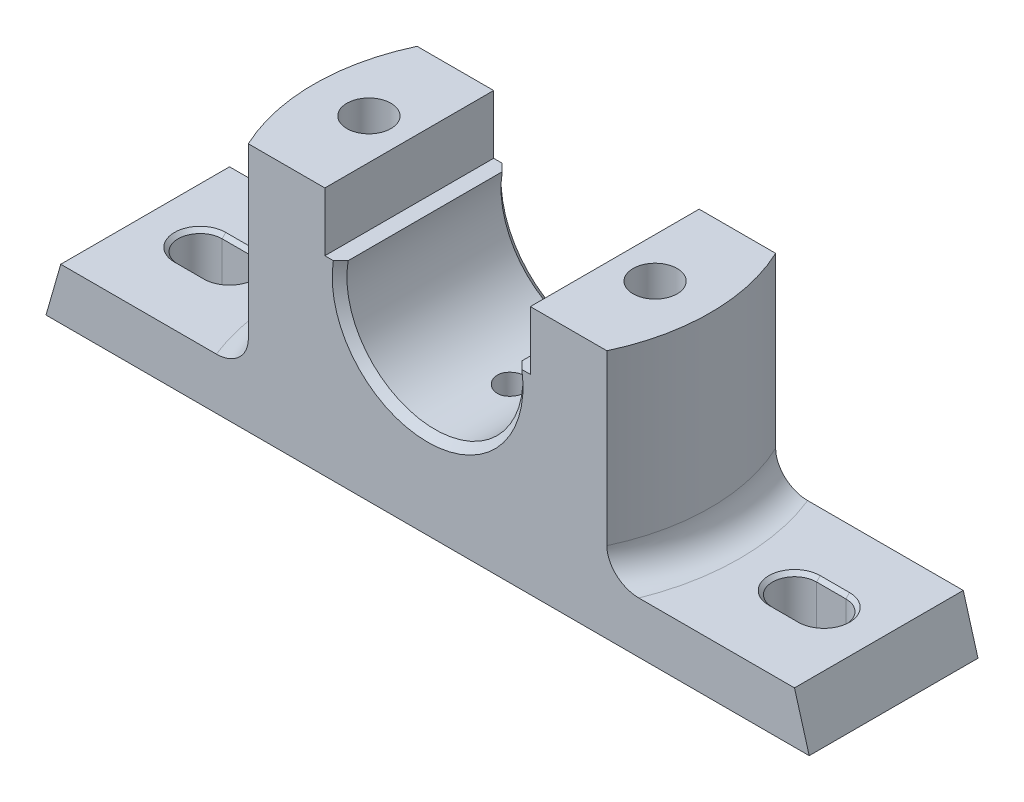
SolidWorks part; units mm, degrees
material "Plain Carbon Steel"
ref_plane "Front Plane" through (0, 0, 0) normal (0, 0, 1) x (1, 0, 0)
ref_plane "Top Plane" through (0, 0, 0) normal (0, 1, 0) x (1, 0, 0)
ref_plane "Right Plane" through (0, 0, 0) normal (1, 0, 0) x (0, 0, -1)
sketch "Sketch1" plane through (0, 0, 0) normal (0, 0, 1) x (1, 0, 0)
  line L0 (-104, 0) -> (104, 0)
  line L1 (-104, 0) -> (-99.9856, 14)
  line L2 (-99.9856, 14) -> (99.9856, 14)
  line L3 (99.9856, 14) -> (104, 0)
  line L4 (0, 0) -> (0, 50.2731) construction
  point P4 (0, 0)
  dimension "D1" = 208
  dimension "D2" = 74
  dimension "D3" = 14
extrude "Boss-Extrude1" add sketch "Sketch1" along normal mid plane 46
sketch "Sketch2" plane through (0, 14, 0) normal (0, 1, 0) x (1, 0, 0)
  line L0 (99.9856, 23) -> (-99.9856, 23) construction
  line L1 (48.8569, 23) -> (-48.8569, 23)
  line L2 (99.9856, -23) -> (-99.9856, -23) construction
  line L3 (48.8569, -23) -> (-48.8569, -23)
  arc A0 (48.8569, -23) -> (48.8569, 23) centre (0, 0) ccw
  arc A1 (-48.8569, 23) -> (-48.8569, -23) centre (0, 0) ccw
  dimension "D1" = 54
extrude "Boss-Extrude2" add sketch "Sketch2" along normal blind 54
sketch "Sketch3" plane through (0, 0, 23) normal (0, 0, 1) x (1, 0, 0)
  line L0 (-28, 68) -> (-28, 52)
  line L1 (-48.8569, 68) -> (48.8569, 68) construction
  line L2 (0, 0) -> (0, 81.0135) construction
  line L3 (-28, 68) -> (28, 68)
  line L4 (28, 68) -> (28, 52)
  line L5 (99.9856, 14) -> (48.8569, 14) construction
  line L6 (-28, 52) -> (-23.6643, 52)
  line L7 (28, 52) -> (23.6643, 52)
  arc A0 (-23.6643, 52) -> (23.6643, 52) centre (0, 48) ccw
  dimension "D1" = 24
  dimension "D2" = 34
  dimension "D3" = 16
  dimension "D4" = 56
extrude "Cut-Extrude1" cut sketch "Sketch3" against normal through all
sketch "Sketch4" plane through (0, 68, 0) normal (0, 1, 0) x (1, 0, 0)
  line L0 (0, 0) -> (0, 39.5903) construction
  circle A0 centre (-39, 0) radius 6
  circle A1 centre (39, 0) radius 6
  dimension "D1" = 12
  dimension "D2" = 78
extrude "Cut-Extrude2" cut sketch "Sketch4" against normal through all
sketch "Sketch5" plane through (0, 0, 0) normal (0, -1, 0) x (1, 0, 0)
  line L1 (-53, -14) -> (-25, -14)
  line L2 (-53, -14) -> (-53, 14)
  line L3 (-53, 14) -> (-25, 14)
  line L4 (-25, -14) -> (-25, 14)
  line L5 (-53, -14) -> (-25, 14) construction
  line L6 (-53, 14) -> (-25, -14) construction
  line L7 (25, -14) -> (53, -14)
  line L8 (25, -14) -> (25, 14)
  line L9 (25, 14) -> (53, 14)
  line L10 (53, -14) -> (53, 14)
  line L11 (25, -14) -> (53, 14) construction
  line L12 (25, 14) -> (53, -14) construction
  point P0 (-39, 0)
  point P6 (39, 0)
  dimension "D1" = 28
  dimension "D2" = 28
  dimension "D3" = 28
  dimension "D4" = 28
extrude "Cut-Extrude3" cut sketch "Sketch5" against normal blind 8
sketch "Sketch6" plane through (0, 14, 0) normal (0, 1, 0) x (1, 0, 0)
  line L0 (0, 0) -> (-87.4734, 0) construction
  line L1 (-85, 0) -> (-77, 0) construction
  line L2 (-85, 6) -> (-77, 6)
  line L3 (-85, -6) -> (-77, -6)
  arc A0 (-85, 6) -> (-85, -6) centre (-85, 0) ccw
  arc A1 (-77, -6) -> (-77, 6) centre (-77, 0) ccw
  point P5 (-81, 0)
  dimension "D1" = 6
  dimension "D2" = 8
  dimension "D3" = 77
extrude "Cut-Extrude4" cut sketch "Sketch6" against normal through all
mirror "Mirror1" about plane through (0, 0, 0) normal (1, 0, 0) of "Cut-Extrude4"
sketch "Sketch7" plane through (0, 68, 0) normal (0, 1, 0) x (1, 0, 0)
  circle A0 centre (0, 0) radius 4
  dimension "D1" = 8
extrude "Cut-Extrude5" cut sketch "Sketch7" against normal blind 54
fillet "Fillet1" radius 8 2 edges at (-54, 14, 0) (54, 14, 0)
chamfer "Chamfer1" distance 2 angle 45 2 edges at (0, 24, 23) (0, 24, -23)
chamfer "Chamfer2" distance 1 angle 45 8 edges at (81, 14, 6) (71, 14, 0) (91, 14, 0) (81, 14, -6) (-71, 14, 0) (-81, 14, -6) (-81, 14, 6) (-91, 14, 0)
